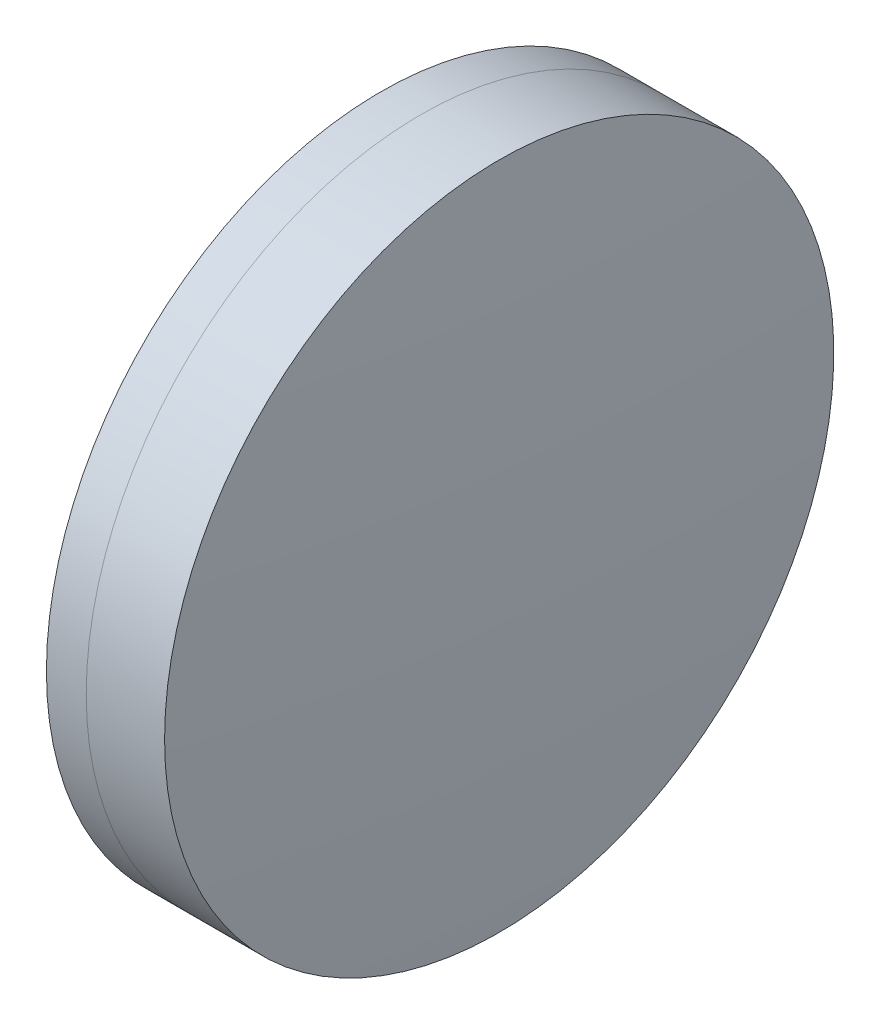
SolidWorks part; units mm, degrees
ref_plane "前视基准面" through (0, 0, 0) normal (0, 0, 1) x (1, 0, 0)
ref_plane "上视基准面" through (0, 0, 0) normal (0, 1, 0) x (1, 0, 0)
ref_plane "右视基准面" through (0, 0, 0) normal (1, 0, 0) x (0, 0, -1)
sketch "草图1" plane through (0, 0, 0) normal (0, 1, 0) x (1, 0, 0)
  line L0 (124.5233, 0) -> (395.1269, 0) construction
  line L1 (252.8463, -15.75) -> (254.7207, -15.75)
  line L2 (252.8463, 15.75) -> (254.7207, 15.75)
  arc A0 (254.7207, -15.75) -> (254.7207, 15.75) centre (180.9032, 0) ccw
  arc A1 (252.8463, 15.75) -> (252.8463, -15.75) centre (351.9232, 0) ccw
  point P10 (251.6022, 0)
  point P11 (256.3822, 0)
  dimension "D3" = 100.321
  dimension "D4" = 75.479
  dimension "D1" = 15.75
  dimension "D2" = 15.75
  dimension "D5" = 4.78
revolve "旋转1" add sketch "草图1" angle 360 about L0
sketch "草图2" plane through (0, 0, 0) normal (0, 1, 0) x (1, 0, 0)
  line L0 (-0.5519, 0) -> (409.4962, 0) construction
  line L2 (254.7207, 15.75) -> (258.4086, 15.75)
  line L3 (254.7207, -15.75) -> (258.4086, -15.75)
  arc A0 (258.4086, -15.75) -> (258.4086, 15.75) centre (26.2392, 0) ccw
  arc A1 (254.7207, -15.75) -> (254.7207, 15.75) centre (180.9032, 0) ccw construction
  arc A2 (254.7207, -15.75) -> (254.7207, 15.75) centre (180.9032, 0) ccw
  point P4 (256.3822, 0)
  point P8 (258.9422, 0)
  dimension "D1" = 232.703
  dimension "D2" = 2.56
revolve "旋转3" add sketch "草图2" angle 360 about L0
